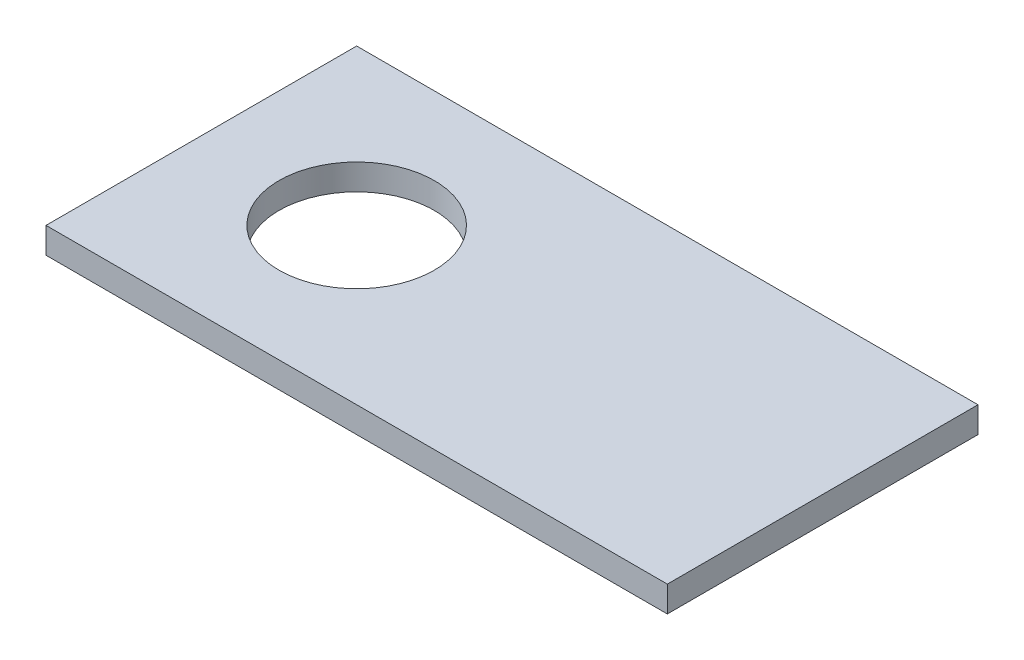
SolidWorks part; units mm, degrees
material "6061-T6 (SS)"
ref_plane "Front Plane" through (0, 0, 0) normal (0, 0, 1) x (1, 0, 0)
ref_plane "Top Plane" through (0, 0, 0) normal (0, 1, 0) x (1, 0, 0)
ref_plane "Right Plane" through (0, 0, 0) normal (1, 0, 0) x (0, 0, -1)
sketch "Sketch1" plane through (0, 0, 0) normal (0, 1, 0) x (1, 0, 0)
  line L0 (-19.05, -1140.9047) -> (-19.05, 56142.4536) construction
  line L1 (19.05, -1141.449) -> (19.05, 56141.9093) construction
  line L3 (-57.15, 19.05) -> (19.05, 19.05)
  line L4 (-57.15, 19.05) -> (-57.15, -19.05)
  line L5 (-57.15, -19.05) -> (19.05, -19.05)
  line L6 (19.05, 19.05) -> (19.05, -19.05)
  line L7 (-57.15, 19.05) -> (19.05, -19.05) construction
  line L8 (-57.15, -19.05) -> (19.05, 19.05) construction
  circle A0 centre (-38.1, 0) radius 9.525
  circle A1 centre (-38.1, 0) radius 12.7 construction
  point P8 (-19.05, 0)
  point P13 (0, 0)
  dimension "D3" = 19.05
  dimension "D4" = 25.4
  dimension "D1" = 19.05
  dimension "D2" = 19.05
  dimension "D5" = 19.05
  dimension "D6" = 38.1
  dimension "D7" = 6.35
extrude "Boss-Extrude1" add sketch "Sketch1" along normal blind 3.175
